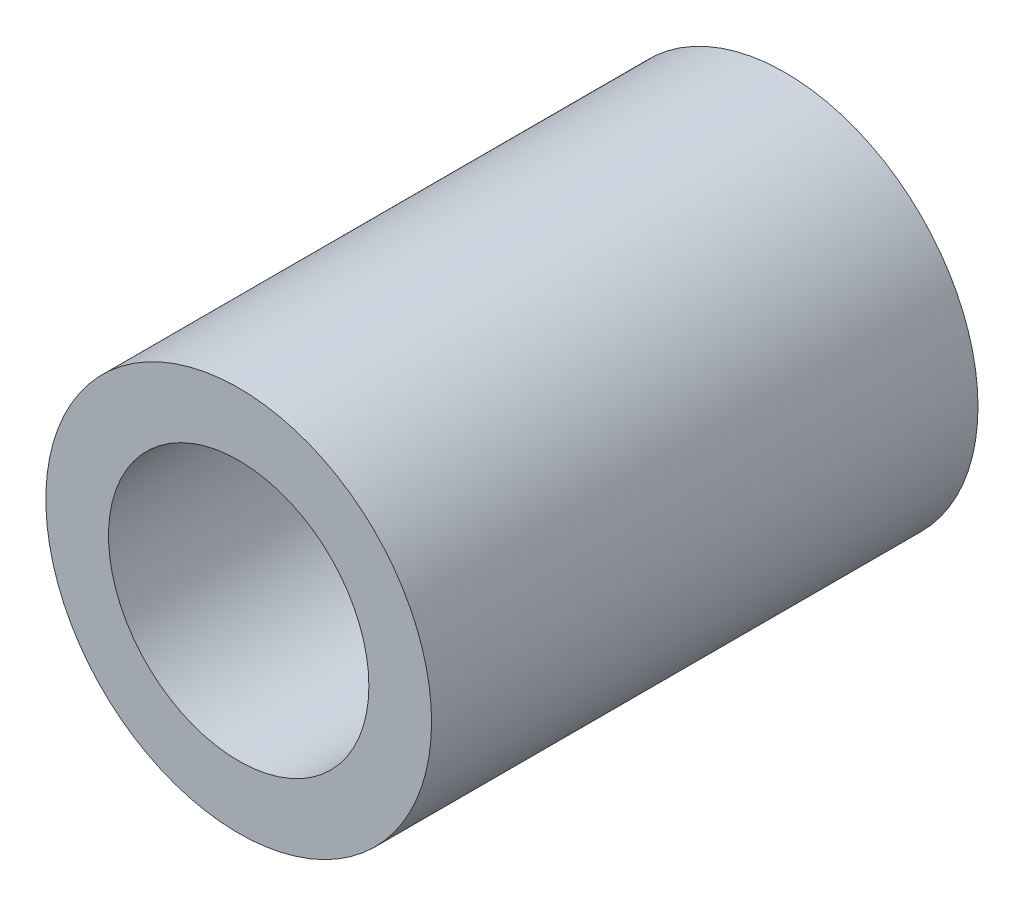
SolidWorks part; units mm, degrees
ref_plane "Plan de face" through (0, 0, 0) normal (0, 0, 1) x (1, 0, 0)
ref_plane "Plan de dessus" through (0, 0, 0) normal (0, 1, 0) x (1, 0, 0)
ref_plane "Plan de droite" through (0, 0, 0) normal (1, 0, 0) x (0, 0, -1)
sketch "Esquisse1" plane through (0, 0, 0) normal (0, 0, 1) x (1, 0, 0)
  circle A0 centre (0, 0) radius 2.025
  circle A1 centre (0, 0) radius 3
  dimension "D1" = 6
  dimension "D2" = 4.05
extrude "Extrusion1" add sketch "Esquisse1" along normal mid plane 8.5
